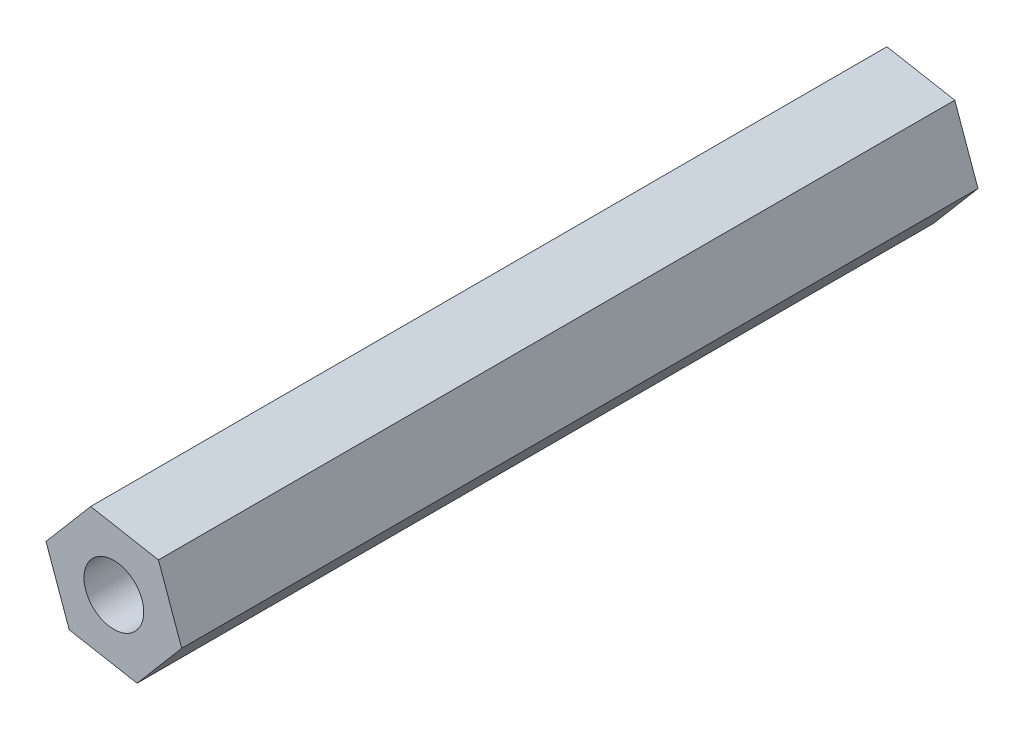
SolidWorks part; units mm, degrees
ref_plane "Plano frontal" through (0, 0, 0) normal (0, 0, 1) x (1, 0, 0)
ref_plane "Plano superior" through (0, 0, 0) normal (0, 1, 0) x (1, 0, 0)
ref_plane "Plano direito" through (0, 0, 0) normal (1, 0, 0) x (0, 0, -1)
sketch "Esboço1" plane through (0, 0, 0) normal (0, 0, 1) x (1, 0, 0)
  line L1 (12.9332, -4.1439) -> (9.5251, -3.5237)
  line L2 (9.5251, -3.5237) -> (7.2839, -6.1651)
  line L3 (7.2839, -6.1651) -> (8.4508, -9.4267)
  line L4 (8.4508, -9.4267) -> (11.8589, -10.0469)
  line L5 (11.8589, -10.0469) -> (14.1001, -7.4055)
  line L6 (14.1001, -7.4055) -> (12.9332, -4.1439)
  circle A0 centre (10.692, -6.7853) radius 3 construction
extrude "Ressalto-extrusão1" add sketch "Esboço1" along normal blind 40
sketch "Esboço4" plane through (0, 0, 0) normal (0, 0, -1) x (-1, 0, 0)
  line L1 (-12.9332, -4.1439) -> (-9.5251, -3.5237) construction
  circle A0 centre (-10.692, -6.7853) radius 1.5
  dimension "D1" = 3
extrude "Corte-extrusão2" cut sketch "Esboço4" against normal blind 40
